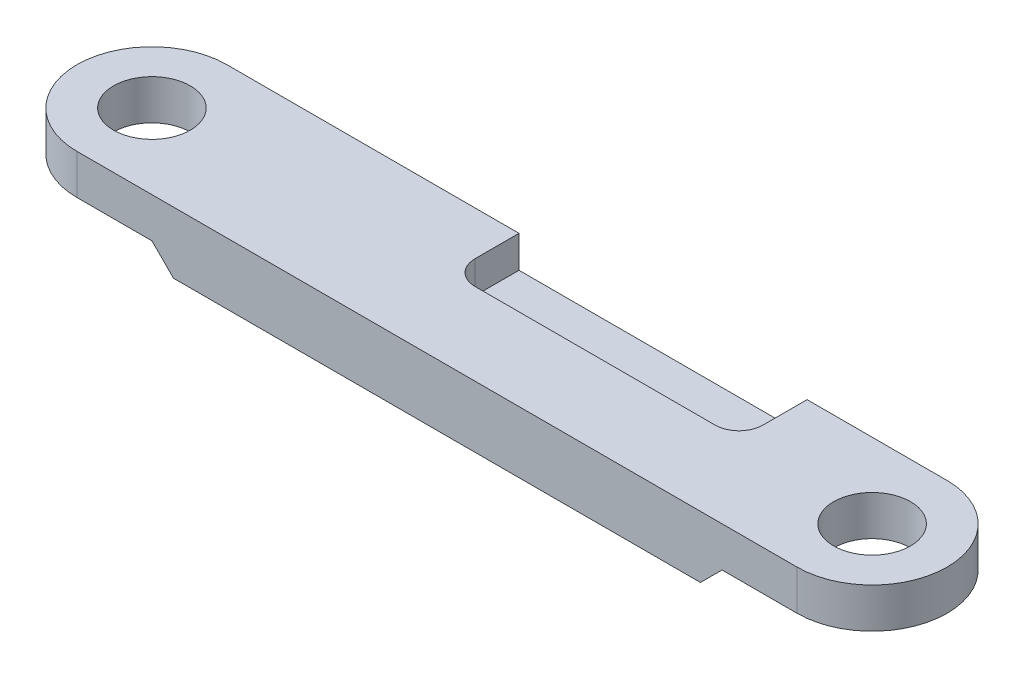
SolidWorks part; units mm, degrees
ref_plane "Plane XZ" through (0, 0, 0) normal (0, 0, 1) x (1, 0, 0)
ref_plane "Plane XY" through (0, 0, 0) normal (0, 1, 0) x (1, 0, 0)
ref_plane "Plane YZ" through (0, 0, 0) normal (1, 0, 0) x (0, 0, -1)
sketch "Sketch1" plane through (0, 0, 0) normal (0, 1, 0) x (1, 0, 0)
  line L0 (0, 2.3813) -> (0, -2.3813) construction
  line L1 (-11.43, 2.3813) -> (11.43, 2.3813)
  line L2 (-11.43, 2.3813) -> (-11.43, -2.3813) construction
  line L3 (-11.43, -2.3813) -> (11.43, -2.3813)
  line L4 (11.43, 2.3813) -> (11.43, -2.3813) construction
  line L5 (-11.43, 0) -> (0, 0) construction
  circle A0 centre (-11.43, 0) radius 1.2192
  circle A1 centre (11.43, 0) radius 1.2192
  arc A2 (-11.43, 2.3813) -> (-11.43, -2.3813) centre (-11.43, 0) ccw
  arc A3 (11.43, 2.3813) -> (11.43, -2.3813) centre (11.43, 0) cw
  dimension "D3" = 2.4384
  dimension "D1" = 4.7625
  dimension "D2" = 22.86
extrude "Boss-Extrude1" add sketch "Sketch1" along normal blind 1.9558
sketch "Sketch3" plane through (0, 0, -2.3813) normal (0, 0, -1) x (-1, 0, 0)
  line L5 (-11.43, 1.9558) -> (11.43, 1.9558) construction
  line L6 (-6.985, 1.9558) -> (2.159, 1.9558)
  line L7 (-6.985, 1.9558) -> (-6.985, 0.9398)
  line L8 (-6.985, 0.9398) -> (2.159, 0.9398)
  line L9 (2.159, 1.9558) -> (2.159, 0.9398)
  line L10 (-11.43, 0) -> (11.43, 0) construction
  line L11 (0, 0) -> (0, -2.4156) construction
  point P8 (0, 0)
  dimension "D1" = 2.159
  dimension "D2" = 1.016
  dimension "D3" = 6.985
extrude "Cut-Extrude1" cut sketch "Sketch3" against normal blind 2.159
fillet "Fillet1" radius 0.762 2 edges at (-2.159, 1.4478, -0.2223) (6.985, 1.4478, -0.2223)
sketch "Sketch4" plane through (0, 0, -2.3813) normal (0, 0, -1) x (-1, 0, 0)
  line L0 (-8.3629, 0) -> (-9.0488, 0.6858)
  line L1 (-11.43, 0) -> (11.43, 0) construction
  line L2 (-9.0488, 0.6858) -> (-14.5911, 0.6858)
  line L3 (-14.5911, 0.6858) -> (-14.5911, 0)
  line L4 (-14.5911, 0) -> (-8.3629, 0)
  line L5 (-11.43, 0) -> (-11.43, -1.555) construction
  line L6 (-12.6492, 0) -> (-10.2108, 0) construction
  line L7 (-11.43, 1.9558) -> (-6.985, 1.9558) construction
  line L8 (0, 0) -> (0, -4.0144) construction
  line L9 (14.5911, 0.6858) -> (14.5911, 0)
  line L10 (9.0488, 0.6858) -> (14.5911, 0.6858)
  line L11 (8.3629, 0) -> (9.0488, 0.6858)
  line L12 (14.5911, 0) -> (8.3629, 0)
  dimension "D1" = 2.3813
  dimension "D2" = 45
  dimension "D3" = 1.27
extrude "Cut-Extrude2" cut sketch "Sketch4" against normal through all
